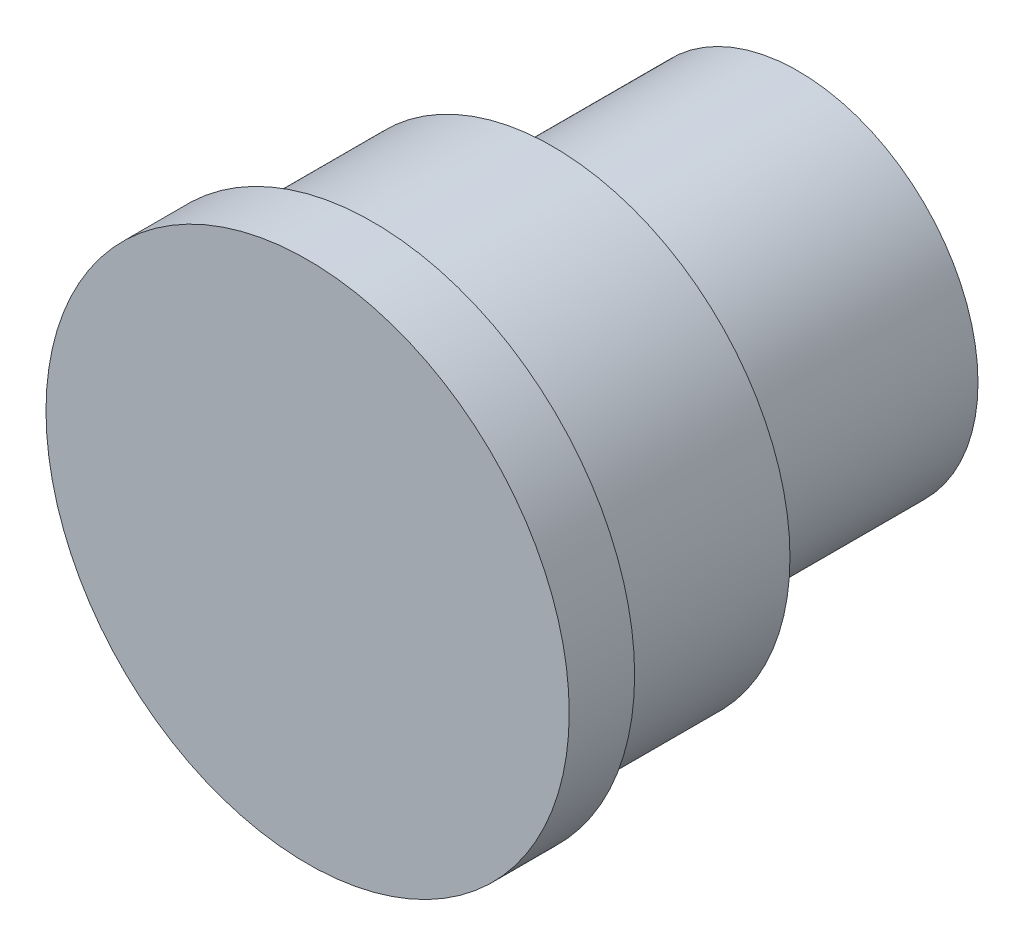
SolidWorks part; units mm, degrees
ref_plane "前视基准面" through (0, 0, 0) normal (0, 0, 1) x (1, 0, 0)
ref_plane "上视基准面" through (0, 0, 0) normal (0, 1, 0) x (1, 0, 0)
ref_plane "右视基准面" through (0, 0, 0) normal (1, 0, 0) x (0, 0, -1)
sketch "草图1" plane through (0, 0, 0) normal (0, 0, 1) x (1, 0, 0)
  circle A0 centre (0, 0) radius 11
extrude "凸台-拉伸1" add sketch "草图1" along normal blind 15
sketch "草图2" plane through (0, 0, 15) normal (0, 0, 1) x (1, 0, 0)
  circle A0 centre (0, 0) radius 14.5
extrude "凸台-拉伸2" add sketch "草图2" along normal blind 11
sketch "草图3" plane through (0, 0, 26) normal (0, 0, 1) x (1, 0, 0)
  circle A1 centre (0, 0) radius 16
  point P0 (0, 0)
extrude "凸台-拉伸3" add sketch "草图3" along normal blind 4
